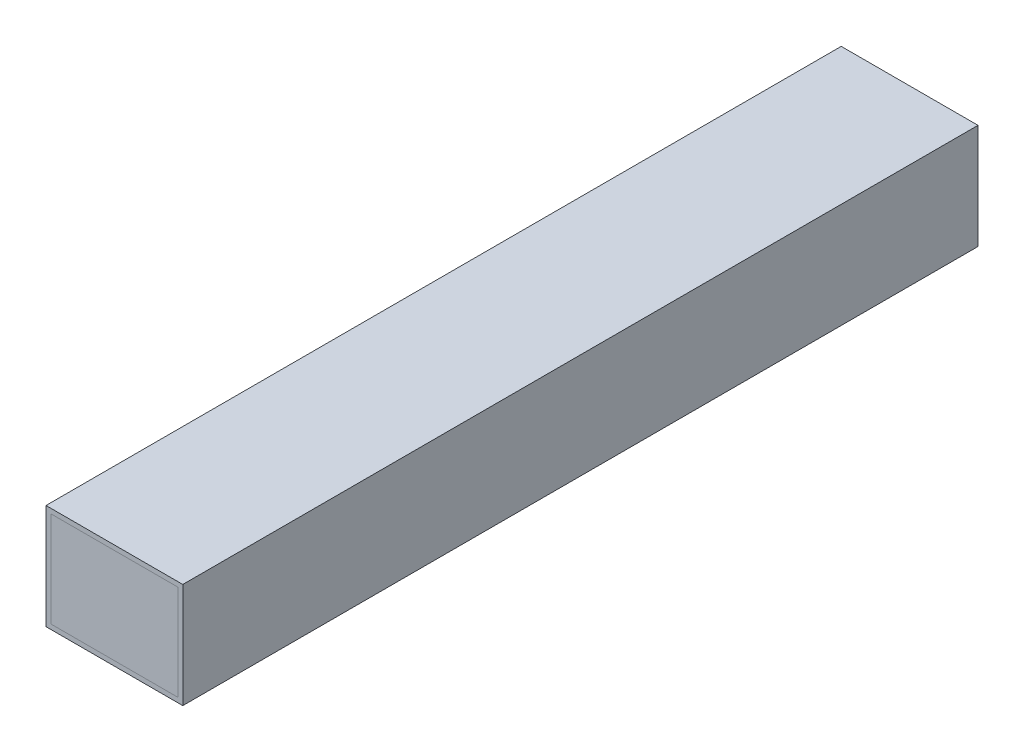
SolidWorks part; units mm, degrees
other "Camera1"
ref_plane "Front Plane" through (0, 0, 0) normal (0, 0, 1) x (1, 0, 0)
ref_plane "Top Plane" through (0, 0, 0) normal (0, 1, 0) x (1, 0, 0)
ref_plane "Right Plane" through (0, 0, 0) normal (1, 0, 0) x (0, 0, -1)
sketch "Sketch1" plane through (0, 0, 0) normal (0, 0, 1) x (1, 0, 0)
  line L1 (-20, 15) -> (20, 15)
  line L2 (-20, 15) -> (-20, -15)
  line L3 (-20, -15) -> (20, -15)
  line L4 (20, 15) -> (20, -15)
  line L5 (-20, 15) -> (20, -15) construction
  line L6 (-20, -15) -> (20, 15) construction
  point P0 (0, 0)
  dimension "D1" = 30
  dimension "D2" = 40
extrude "Extrude-Thin1" add sketch "Sketch1" along normal mid plane 250 thin thin type one direction wall 1.5
sketch "Sketch2" plane through (0, 0, 0) normal (1, 0, 0) x (0, 0, -1)
  line L1 (15, -15) -> (-15, -15)
  line L2 (15, -15) -> (15, -16)
  line L3 (15, -16) -> (-15, -16)
  line L4 (-15, -15) -> (-15, -16)
  line L5 (15, -15) -> (-15, -16) construction
  line L6 (15, -16) -> (-15, -15) construction
  line L9 (-125, -15) -> (125, -15) construction
  line L11 (-25, -15) -> (-55, -15)
  line L12 (-25, -15) -> (-25, -16)
  line L13 (-25, -16) -> (-55, -16)
  line L14 (-55, -15) -> (-55, -16)
  line L15 (25, -15) -> (55, -15)
  line L16 (25, -15) -> (25, -16)
  line L17 (25, -16) -> (55, -16)
  line L18 (55, -15) -> (55, -16)
  point P0 (0, -15.5)
  dimension "D1" = 30
  dimension "D2" = 1
  dimension "D3" = 10
  dimension "D4" = 10
  dimension "D5" = 30
  dimension "D6" = 30
extrude "Boss-Extrude1" add sketch "Sketch2" along normal mid plane 40 separate body
sketch "Sketch3" plane through (0, 0, 0) normal (0, 1, 0) x (1, 0, 0)
  line L0 (-7.6533, 40.7235) -> (7.6533, 40.7235)
  arc A0 (7.6533, 40.7235) -> (-7.6533, 40.7235) centre (0, 40.7235) ccw
revolve "Revolve1" add sketch "Sketch3" angle 360 about L0
sketch "Sketch5" plane through (0, 0, 0) normal (0, 1, 0) x (1, 0, 0)
  line L0 (0, -100) -> (-2.6401, -90.0507)
  line L6 (0, -100) -> (0, 100)
  line L7 (0, 100) -> (-0.3, 100)
  line L8 (-0.3, -90.0007) -> (-0.3, 100)
  line L9 (-2.6401, -90.0507) -> (-0.35, -90.0507)
  arc A0 (-0.35, -90.0507) -> (-0.3, -90.0007) centre (-0.35, -90.0007) ccw
  dimension "D2" = 0.05
  dimension "D1" = 0.3
  dimension "D3" = 200
  dimension "D4" = 100
revolve "Revolve2" add sketch "Sketch5" angle 360 about L6
sketch "Sketch6" plane through (0, 0, 0) normal (0, 0, 1) x (1, 0, 0)
  line L1 (-20, 15) -> (19.9967, 15)
  line L2 (-20, 15) -> (-20, -16.0006)
  line L3 (-20, -16.0006) -> (19.9967, -16.0006)
  line L4 (19.9967, 15) -> (19.9967, -16.0006)
  point P5 (19.9967, -16.0006)
extrude "Boss-Extrude2" add sketch "Sketch6" along normal mid plane 250 separate body
